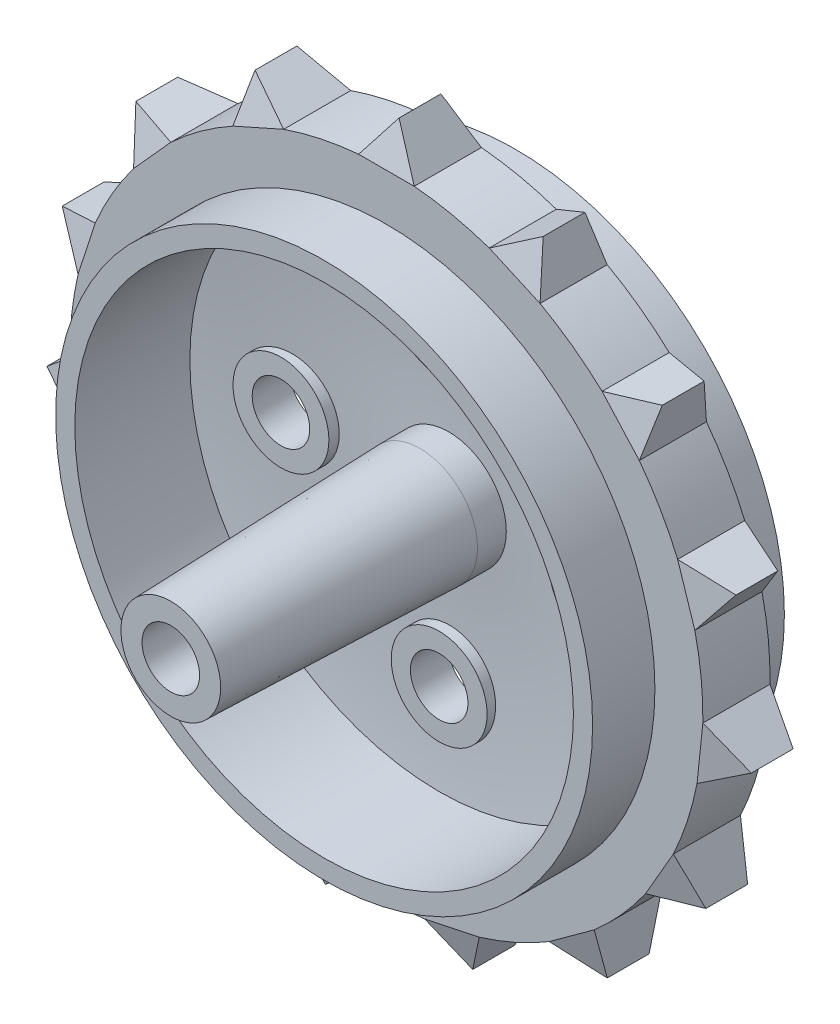
SolidWorks part; units mm, degrees
ref_plane "Front Plane" through (0, 0, 0) normal (0, 0, 1) x (1, 0, 0)
ref_plane "Top Plane" through (0, 0, 0) normal (0, 1, 0) x (1, 0, 0)
ref_plane "Right Plane" through (0, 0, 0) normal (1, 0, 0) x (0, 0, -1)
sketch "Sketch1" plane through (0, 0, 0) normal (1, 0, 0) x (0, 0, -1)
  line L0 (-5, 13) -> (1, 13)
  line L1 (5, 13) -> (5, 14)
  line L2 (5, 14) -> (1.75, 14)
  line L3 (0, -13.0784) -> (0, 40.9695) construction
  line L4 (-19.3836, 0) -> (38.42, 0) construction
  line L5 (1.75, 14) -> (1.75, 16.5)
  line L6 (1.75, 16.5) -> (-1.75, 16.5)
  line L7 (-1.75, 14) -> (-1.75, 16.5)
  line L8 (-5, 14) -> (-1.75, 14)
  line L9 (-5, 13) -> (-5, 14)
  line L10 (0, 1.5) -> (7, 1.5)
  line L11 (7, 1.5) -> (7, 3)
  line L12 (7, 3) -> (2.5, 3)
  line L13 (0, 3) -> (-12.9938, 2.6)
  line L14 (-12.9938, 2.6) -> (-12.9938, 1.5)
  line L15 (-12.9938, 1.5) -> (0, 1.5)
  line L16 (2, 13) -> (5, 13)
  line L17 (1.5, 3) -> (0, 3)
  arc A0 (2.5, 3) -> (2, 13) centre (-53.8315, 5.1959) ccw
  arc A1 (1.5, 3) -> (1, 13) centre (-54.8315, 5.1959) ccw
  point P12 (0, 16.5)
  point P15 (0, 13)
  dimension "D1" = 1
  dimension "D2" = 5
  dimension "D3" = 13
  dimension "D4" = 1.75
  dimension "D5" = 2.5
  dimension "D6" = 1.5
  dimension "D7" = 1.5
  dimension "D8" = 7
  dimension "D9" = 13
  dimension "D10" = 4.5
  dimension "D11" = 3
  dimension "D12" = 1
  dimension "D13" = 1.1
revolve "Revolve1" add sketch "Sketch1" angle 360 about L4
sketch "Sketch4" plane through (0, 0, -7) normal (0, 0, -1) x (-1, 0, 0)
  line L0 (0, 0) -> (0, 16.5) construction
  line L1 (-19.619, 0) -> (23.2359, 0) construction
  circle A0 centre (0, 8.25) radius 1.5
  circle A1 centre (0, 0) radius 16.5 construction
  circle A2 centre (8.25, 0) radius 1.5
  circle A3 centre (0, -8.25) radius 1.5
  circle A4 centre (-8.25, 0) radius 1.5
  point P19 (0, 0)
  dimension "D1" = 3
  dimension "D2" = 4
extrude "Cut-Extrude1" cut sketch "Sketch4" against normal blind 14.25
ref_plane "Plane1" through (0, 0, -2.5) normal (0, 0, -1) x (-1, 0, 0)
sketch "Sketch5" plane through (0, 0, -2.5) normal (0, 0, -1) x (-1, 0, 0)
  circle A0 centre (0, 8.25) radius 1.5
  circle A1 centre (0, 8.25) radius 2.5
  circle A2 centre (8.25, 0) radius 1.5
  circle A3 centre (8.25, 0) radius 2.5
  circle A4 centre (0, -8.25) radius 1.5
  circle A5 centre (0, -8.25) radius 2.5
  circle A6 centre (-8.25, 0) radius 1.5
  circle A7 centre (-8.25, 0) radius 2.5
  point P20 (0, 0)
  dimension "D1" = 1
  dimension "D2" = 4
extrude "Boss-Extrude3" add sketch "Sketch5" against normal blind 1.5 and the other way blind 0.5
sketch "Sketch6" plane through (0, 0, -7) normal (0, 0, -1) x (-1, 0, 0)
  circle A0 centre (0, 0) radius 3
extrude "Boss-Extrude4" add sketch "Sketch6" along normal blind 1
fillet "Fillet2" radius 0.25 1 edges at (-3, 0, -8)
sketch "Sketch7" plane through (0, 0, -3) normal (0, 0, -1) x (-1, 0, 0)
  circle A0 centre (0, 8.25) radius 2.5 construction
  circle A1 centre (-8.25, 0) radius 2.5 construction
  circle A2 centre (0, -8.25) radius 2.5 construction
  circle A3 centre (8.25, 0) radius 2.5 construction
  circle A4 centre (0, 0) radius 3 construction
  arc A5 (-1.7928, 6.5076) -> (1.7928, 6.5076) centre (0, 8.25) ccw
  arc A6 (-6.5076, -1.7928) -> (-6.5076, 1.7928) centre (-8.25, 0) ccw
  arc A7 (1.7928, -6.5076) -> (-1.7928, -6.5076) centre (0, -8.25) ccw
  arc A8 (6.5076, 1.7928) -> (6.5076, -1.7928) centre (8.25, 0) ccw
  circle A9 centre (0, 0) radius 3
  arc A10 (-6.5076, -1.7928) -> (-1.7928, -6.5076) centre (0, 0) ccw
  arc A11 (6.5076, 1.7928) -> (1.7928, 6.5076) centre (0, 0) ccw
  arc A12 (-1.7928, 6.5076) -> (-6.5076, 1.7928) centre (0, 0) ccw
  arc A13 (1.7928, -6.5076) -> (6.5076, -1.7928) centre (0, 0) ccw
extrude "Boss-Extrude5" add sketch "Sketch7" against normal blind 1
sketch "Sketch8" plane through (0, 0, -1.75) normal (0, 0, -1) x (-1, 0, 0)
  line L0 (0, -1.2564) -> (0, 1.6436) construction
  line L1 (0, 16.5) -> (-17.9696, 16.5) construction
  line L2 (-17.9696, 16.5) -> (16.1129, 16.5) construction
  line L3 (-1.45, 16.4362) -> (1.45, 16.4362)
  line L4 (0, -5.3434) -> (0, 24.2527) construction
  line L5 (-1.45, 16.4362) -> (0, 18.4675)
  line L6 (0, 18.4675) -> (1.45, 16.4362)
  circle A0 centre (0, 0) radius 16.5 construction
  dimension "D1" = 2.9
extrude "Boss-Extrude6" add sketch "Sketch8" against normal up to surface (3.5 mm away) up to face at (14, 0, 1.75)
sketch "Sketch9" plane through (0, 0, 0) normal (1, 0, 0) x (0, 0, -1)
  line L0 (-1.75, 16.4362) -> (-1.09, 18.4675)
  line L1 (-1.75, 18.4675) -> (1.75, 18.4675) construction
  line L2 (-1.09, 18.4675) -> (-1.75, 18.4675)
  line L3 (-1.75, 18.4675) -> (-1.75, 16.4362)
  line L4 (0, 18.9564) -> (0, 16.3051) construction
  line L5 (1.75, 18.4675) -> (1.75, 16.4362)
  line L6 (1.09, 18.4675) -> (1.75, 18.4675)
  line L7 (1.75, 16.4362) -> (1.09, 18.4675)
  dimension "D1" = 18
extrude "Cut-Extrude2" cut sketch "Sketch9" against normal up to vertex and the other way up to vertex
pattern_circular "CirPattern1" count 15 over 360 about axis through (0, 0, 0) along (0, 0, 1) of "Cut-Extrude2", "Boss-Extrude4", "Boss-Extrude6"
